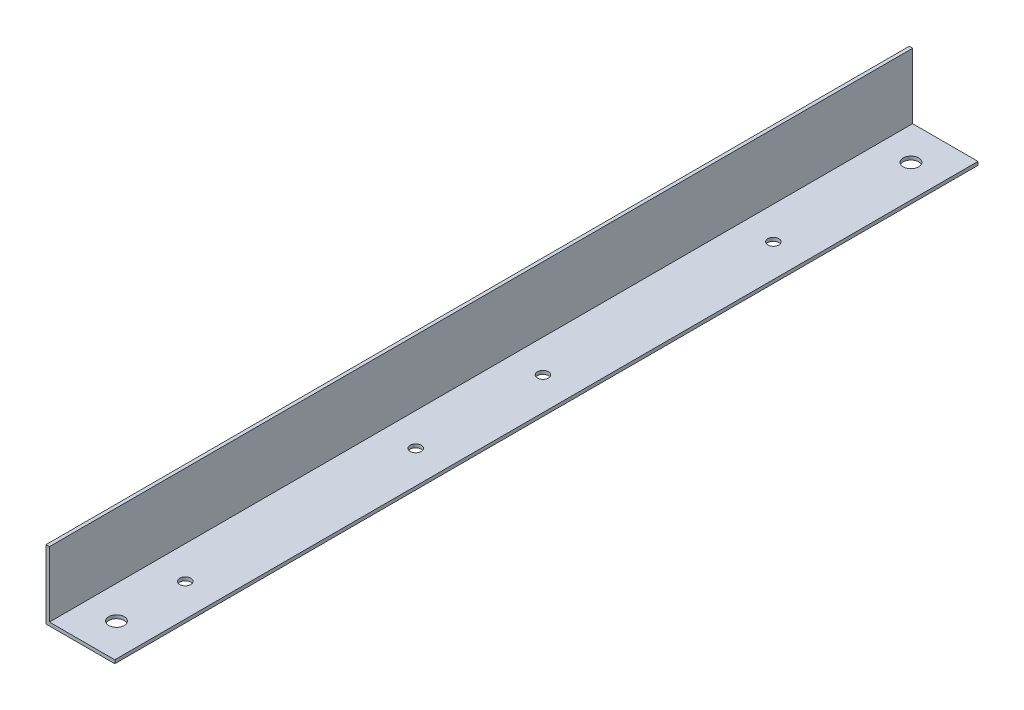
SolidWorks part; units mm, degrees
material "1060 Сплав"
ref_plane "Спереди" through (0, 0, 0) normal (0, 0, 1) x (1, 0, 0)
ref_plane "Сверху" through (0, 0, 0) normal (0, 1, 0) x (1, 0, 0)
ref_plane "Справа" through (0, 0, 0) normal (1, 0, 0) x (0, 0, -1)
sketch "Эскиз1" plane through (0, 0, 0) normal (0, 0, 1) x (1, 0, 0)
  line L0 (0, 0) -> (0, 20)
  line L1 (0, 20) -> (1, 20)
  line L2 (1, 20) -> (1, 1)
  line L3 (1, 1) -> (20, 1)
  line L4 (20, 1) -> (20, 0)
  line L5 (20, 0) -> (0, 0)
  dimension "D1" = 20
  dimension "D2" = 1
extrude "Бобышка-Вытянуть1" add sketch "Эскиз1" along normal blind 251
sketch "Эскиз2" plane through (0, 1, 0) normal (0, 1, 0) x (1, 0, 0)
  line L0 (10.5, 0) -> (10.5, -251) construction
  line L1 (20, 0) -> (1, 0) construction
  line L2 (20, -251) -> (1, -251) construction
  line L3 (20, -125.5) -> (10.5, -125.5) construction
  line L4 (20, -251) -> (20, 0) construction
  line L5 (10.5, -50) -> (10.5, -117) construction
  line L6 (20, -83.5) -> (10.5, -83.5) construction
  line L7 (1, -40) -> (20, -40) construction
  line L8 (1, -251) -> (1, 0) construction
  line L9 (1, -231) -> (20, -231) construction
  circle A0 centre (10.5, -50) radius 1.6
  circle A1 centre (10.5, -117) radius 1.6
  circle A2 centre (10.5, -221) radius 1.6
  circle A3 centre (10.5, -154) radius 1.6
  point P17 (10.5, -83.5)
  dimension "D1" = 3.2
  dimension "D2" = 3.2
  dimension "D3" = 67
  dimension "D6" = 10
  dimension "D8" = 3.2
  dimension "D10" = 67
  dimension "D4" = 125.5
  dimension "D5" = 40
  dimension "D7" = 20
  dimension "D9" = 10
extrude "Вырез-Вытянуть1" cut sketch "Эскиз2" against normal through all
sketch "Эскиз3" plane through (0, 1, 0) normal (0, 1, 0) x (1, 0, 0)
  line L0 (10.5, 0) -> (10.5, -251) construction
  line L1 (20, 0) -> (1, 0) construction
  line L2 (20, -251) -> (1, -251) construction
  circle A0 centre (10.5, -241) radius 2.25
  circle A1 centre (10.5, -10) radius 2.25
  dimension "D1" = 4.5
  dimension "D2" = 10
  dimension "D3" = 4.5
  dimension "D4" = 10
extrude "Вырез-Вытянуть2" cut sketch "Эскиз3" against normal through all
